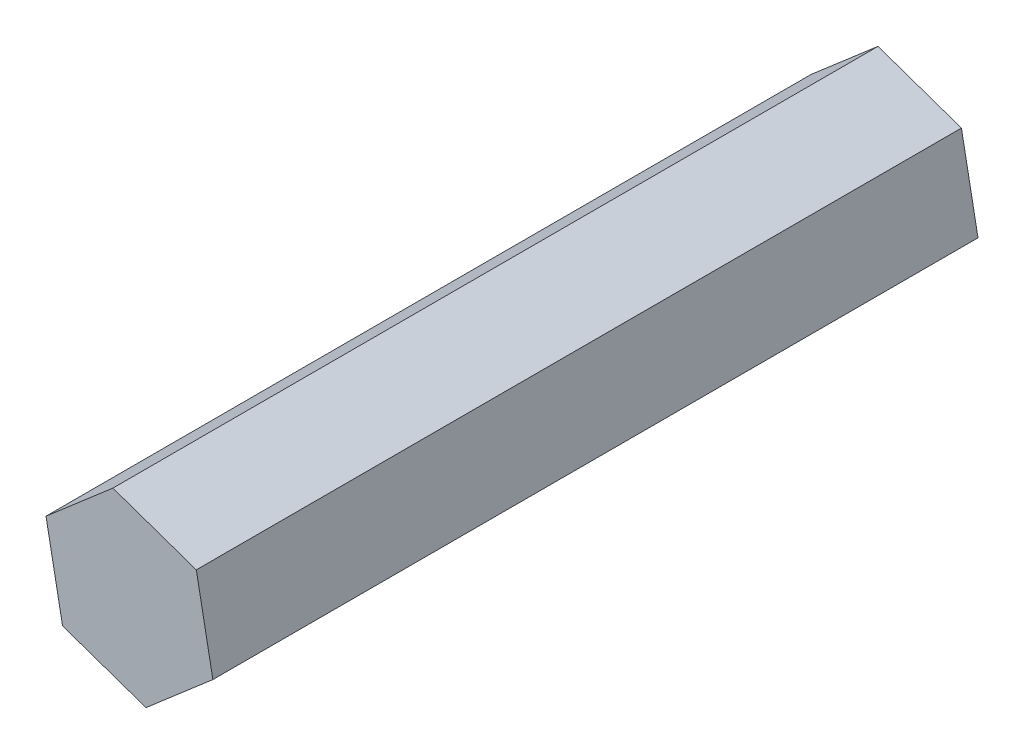
SolidWorks part; units mm, degrees
ref_plane "Front Plane" through (0, 0, 0) normal (0, 0, 1) x (1, 0, 0)
ref_plane "Top Plane" through (0, 0, 0) normal (0, 1, 0) x (1, 0, 0)
ref_plane "Right Plane" through (0, 0, 0) normal (1, 0, 0) x (0, 0, -1)
sketch "Sketch1" plane through (0, 0, 0) normal (0, 0, 1) x (1, 0, 0)
  line L1 (5.5502, 4.7915) -> (-1.3745, 7.2024)
  line L2 (-1.3745, 7.2024) -> (-6.9247, 2.4108)
  line L3 (-6.9247, 2.4108) -> (-5.5502, -4.7915)
  line L4 (-5.5502, -4.7915) -> (1.3745, -7.2024)
  line L5 (1.3745, -7.2024) -> (6.9247, -2.4108)
  line L6 (6.9247, -2.4108) -> (5.5502, 4.7915)
  circle A0 centre (0, 0) radius 6.35 construction
  dimension "D1" = 12.7
extrude "Boss-Extrude1" add sketch "Sketch1" along normal blind 63.5
